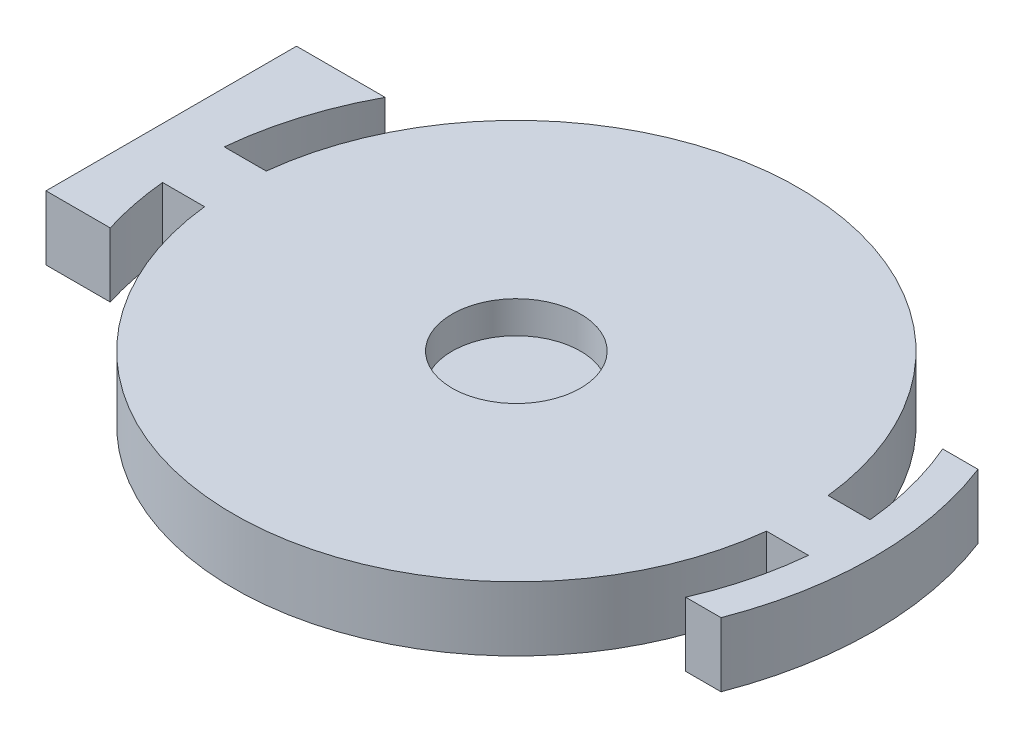
SolidWorks part; units mm, degrees
ref_plane "Front Plane" through (0, 0, 0) normal (0, 0, 1) x (1, 0, 0)
ref_plane "Top Plane" through (0, 0, 0) normal (0, 1, 0) x (1, 0, 0)
ref_plane "Right Plane" through (0, 0, 0) normal (1, 0, 0) x (0, 0, -1)
sketch "Sketch1" plane through (0, 0, 0) normal (0, 1, 0) x (1, 0, 0)
  line L0 (22, 0) -> (-21.8687, 0) construction
  line L1 (-25.8687, 2.4) -> (-21.8687, 2.4)
  line L2 (-25.8687, 2.4) -> (-25.8687, -2.4)
  line L3 (-25.8687, -2.4) -> (-21.8687, -2.4)
  line L4 (-21.8687, 2.4) -> (-21.8687, -2.4)
  line L5 (-25.8687, 0) -> (-21.8687, 0) construction
  line L6 (21.8687, 2.4) -> (25.1357, 2.4)
  line L7 (21.8687, 2.4) -> (21.8687, -2.4)
  line L8 (21.8687, -2.4) -> (25.1357, -2.4)
  line L10 (21.8687, 0) -> (27.7965, 0) construction
  line L11 (23.1854, 10) -> (25.9354, 10)
  line L12 (23.1854, -10) -> (25.9354, -10)
  circle A0 centre (0, 0) radius 22
  arc A2 (25.9354, -10) -> (25.9354, 10) centre (0, 0) ccw
  arc A9 (-25.1357, 2.4) -> (-25.1357, -2.4) centre (0, 0) ccw
  arc A10 (23.1854, -10) -> (25.1357, -2.4) centre (0, 0) ccw
  arc A11 (25.1357, 2.4) -> (23.1854, 10) centre (0, 0) ccw
  dimension "D1" = 44
  dimension "D9" = 50.5
  dimension "D2" = 4
  dimension "D3" = 4.8
  dimension "D5" = 4.8
  dimension "D6" = 20
  dimension "D7" = 10
  dimension "D8" = 2.75
extrude "Boss-Extrude1" add sketch "Sketch1" along normal blind 5 contours L7 A0 L4 | A0 L1 L2 L3
sketch "Sketch2" plane through (0, 5, 0) normal (0, 1, 0) x (1, 0, 0)
  line L0 (0, 0) -> (-25.25, 0) construction
  line L1 (-29.1104, 12) -> (-22.2163, 12)
  line L2 (-29.1104, 12) -> (-29.1104, -7.5)
  line L3 (-29.1104, -7.5) -> (-24.1104, -7.5)
  arc A1 (-22.2163, 12) -> (-24.1104, -7.5) centre (0, 0) ccw
  dimension "D3" = 50.5
  dimension "D1" = 7.5
  dimension "D2" = 5
  dimension "D4" = 12
extrude "Boss-Extrude2" add sketch "Sketch2" against normal blind 5
sketch "Sketch3" plane through (0, 5, 0) normal (0, 1, 0) x (1, 0, 0)
  circle A0 centre (0, 0) radius 5
  dimension "D1" = 10
extrude "Cut-Extrude1" cut sketch "Sketch3" against normal blind 2.5
